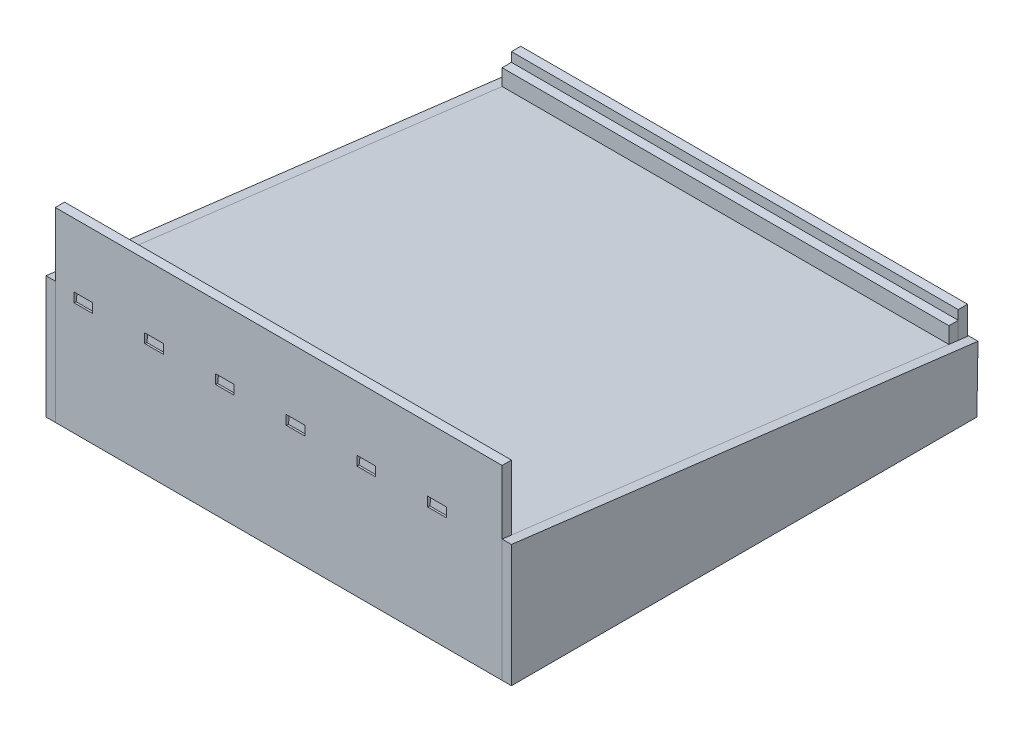
SolidWorks part; units mm, degrees
ref_plane "Front Plane" through (0, 0, 0) normal (0, 0, 1) x (1, 0, 0)
ref_plane "Top Plane" through (0, 0, 0) normal (0, 1, 0) x (1, 0, 0)
ref_plane "Right Plane" through (0, 0, 0) normal (1, 0, 0) x (0, 0, -1)
sketch "Sketch1" plane through (0, 0, 0) normal (0, 1, 0) x (1, 0, 0)
  line L1 (0, 0) -> (304.8, 0)
  line L2 (0, 0) -> (0, 304.8)
  line L3 (0, 304.8) -> (304.8, 304.8)
  line L4 (304.8, 0) -> (304.8, 304.8)
  dimension "D1" = 304.8
  dimension "D2" = 304.8
extrude "Boss-Extrude1" add sketch "Sketch1" along normal blind 6.35 contours L2 L3 L4 L1
sketch "Sketch2" plane through (0, 0, 0) normal (0, 0, 1) x (1, 0, 0)
  line L1 (0, 0) -> (304.8, 0)
  line L2 (0, 0) -> (0, 127)
  line L3 (0, 127) -> (304.8, 127)
  line L4 (304.8, 0) -> (304.8, 127)
  dimension "D1" = 127
  dimension "D2" = 304.8
extrude "Boss-Extrude2" add sketch "Sketch2" along normal blind 6.35
sketch "Sketch4" plane through (0, 0, -304.8) normal (0, 0, -1) x (-1, 0, 0)
  line L0 (0, 127) -> (0, 6.35) construction
  line L1 (-304.8, 0) -> (0, 0)
  line L2 (-304.8, 0) -> (-304.8, 38.1)
  line L3 (-304.8, 38.1) -> (0, 38.1)
  line L4 (0, 0) -> (0, 38.1)
  dimension "D1" = 38.1
extrude "Boss-Extrude3" add sketch "Sketch4" along normal blind 6.35
sketch "Sketch7" plane through (0, 38.1, 0) normal (0, 1, 0) x (1, 0, 0)
  line L1 (0, 304.8) -> (304.8, 304.8)
  line L2 (0, 304.8) -> (0, 0)
  line L3 (0, 0) -> (304.8, 0)
  line L4 (304.8, 304.8) -> (304.8, 0)
extrude "Boss-Extrude4" add sketch "Sketch7" against normal blind 6.35
ref_plane "Plane2" through (0, 75.1711, -9.2299) normal (0, 0.9925, -0.1219) x (1, 0, 0)
sketch "Sketch10" plane through (0, 75.1711, -9.2299) normal (0, 0.9925, -0.1219) x (1, 0, 0)
  line L1 (0, 304.1875) -> (304.8, 304.1875)
  line L2 (0, 304.1875) -> (0, -13.3125)
  line L3 (0, -13.3125) -> (304.8, -13.3125)
  line L4 (304.8, 304.1875) -> (304.8, -13.3125)
  dimension "D1" = 304.8
  dimension "D2" = 317.5
extrude "Boss-Extrude6" add sketch "Sketch10" along normal blind 6.35 separate body
sketch "Sketch16" plane through (0, 75.1711, -9.2299) normal (0, 0.9925, -0.1219) x (1, 0, 0)
  line L0 (0, -6.3027) -> (0, 308.8307) construction
  line L1 (12.7, -14.1601) -> (25.4, -14.1601)
  line L2 (12.7, -14.1601) -> (12.7, -21.7801)
  line L3 (12.7, -21.7801) -> (25.4, -21.7801)
  line L4 (25.4, -14.1601) -> (25.4, -21.7801)
  line L5 (304.8, -21.7801) -> (0, -21.7801) construction
  dimension "D1" = 7.62
  dimension "D2" = 12.7
  dimension "D3" = 12.7
  dimension "D4" = 0
extrude "Cut-Extrude3" cut sketch "Sketch16" along normal blind 6.35
pattern_linear "LPattern1" count 6 spacing 48.26 along (1, 0, 0) of "Cut-Extrude3"
sketch "Sketch22" plane through (0, 0, 0) normal (1, 0, 0) x (0, 0, -1)
  line L0 (-6.35, 0) -> (-6.35, 83.4818)
  line L1 (-6.35, 83.4818) -> (311.9239, 44.4027)
  line L2 (311.9239, 44.4027) -> (311.15, 0)
  line L3 (311.15, 0) -> (-6.35, 0)
extrude "Boss-Extrude23" add sketch "Sketch22" against normal blind 6.35 separate body
pattern_linear "LPattern3" count 2 spacing 311.15 along (1, 0, 0) of "Boss-Extrude23"
sketch "Sketch23" plane through (0, 0, -311.15) normal (0, 0, -1) x (-1, 0, 0)
  line L0 (0, 44.4027) -> (0, 83.0962) construction
  line L1 (-304.8, 38.1) -> (0, 38.1)
  line L2 (-304.8, 38.1) -> (-304.8, 63.5)
  line L3 (-304.8, 63.5) -> (0, 63.5)
  line L4 (0, 38.1) -> (0, 63.5)
  dimension "D1" = 304.8
  dimension "D2" = 25.4
extrude "Boss-Extrude24" add sketch "Sketch23" against normal blind 6.35 separate body
pattern_linear "LPattern4" count 2 spacing 6.35 along (0, 0, 1) of "Boss-Extrude24"
sketch "Sketch24" plane through (0, 0, -298.45) normal (0, 0, 1) x (1, 0, 0)
  line L0 (0, 38.1) -> (0, 63.5) construction
  line L1 (304.8, 63.5) -> (0, 63.5)
  line L2 (304.8, 63.5) -> (304.8, 57.15)
  line L3 (304.8, 57.15) -> (0, 57.15)
  line L4 (0, 63.5) -> (0, 57.15)
  dimension "D1" = 6.35
extrude "Cut-Extrude4" cut sketch "Sketch24" against normal blind 6.35
